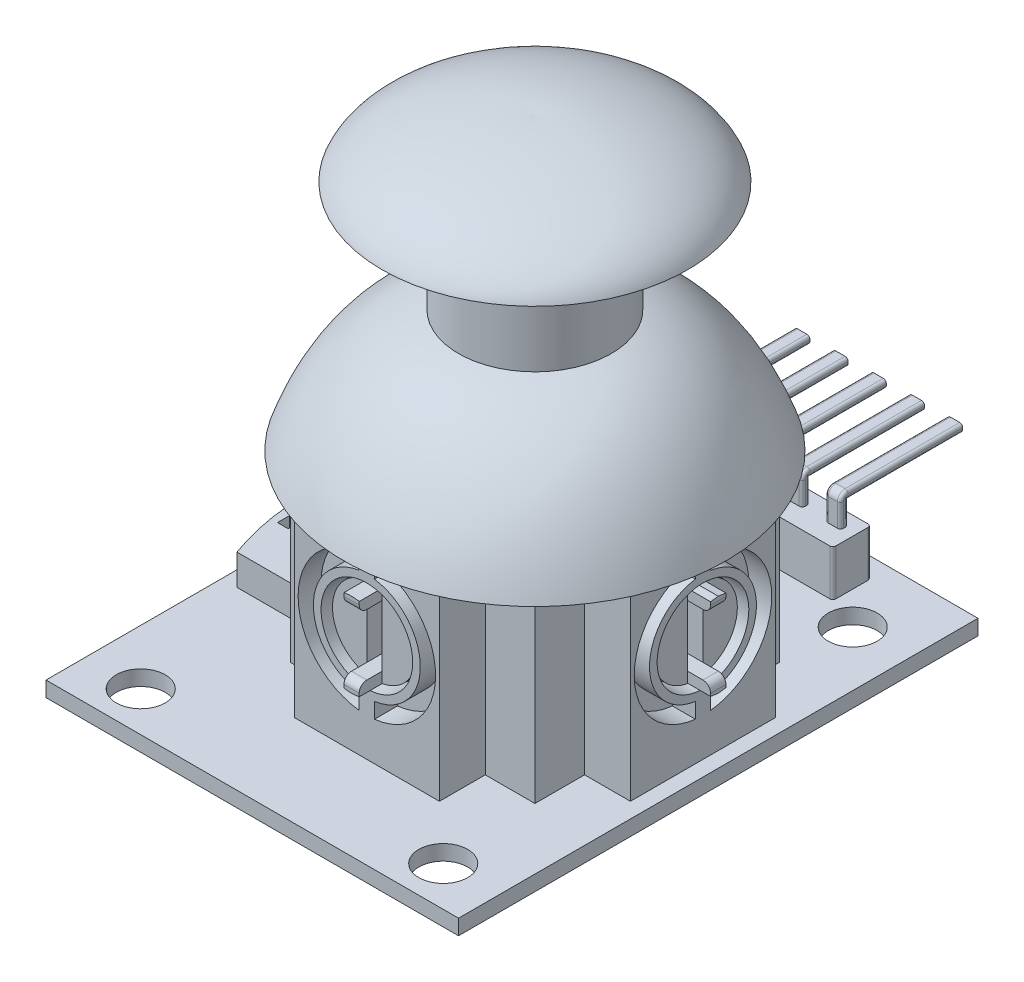
SolidWorks part; units mm, degrees
ref_plane "Ön Düzlem" through (0, 0, 0) normal (0, 0, 1) x (1, 0, 0)
ref_plane "Üst Düzlem" through (0, 0, 0) normal (0, 1, 0) x (1, 0, 0)
ref_plane "Sağ Düzlem" through (0, 0, 0) normal (1, 0, 0) x (0, 0, -1)
sketch "Çizim1" plane through (0, 0, 0) normal (0, 1, 0) x (1, 0, 0)
  line L0 (-13.5, -14.4) -> (13.5, -14.4) construction
  line L1 (-13.5, 17) -> (13.5, 17)
  line L2 (-13.5, 17) -> (-13.5, -17)
  line L3 (-13.5, -17) -> (13.5, -17)
  line L4 (13.5, 17) -> (13.5, -17)
  line L5 (-13.5, 17) -> (13.5, -17) construction
  line L6 (-13.5, -17) -> (13.5, 17) construction
  line L7 (-9.9, 17) -> (-9.9, -17) construction
  line L8 (0, 17) -> (0, -17) construction
  line L9 (-13.5, 12.4) -> (13.5, 12.4) construction
  circle A0 centre (-9.9, -14.4) radius 1.6
  circle A1 centre (9.9, -14.4) radius 1.6
  circle A2 centre (-9.9, 12.4) radius 1.6
  circle A3 centre (9.9, 12.4) radius 1.6
  point P0 (0, 0)
  dimension "D5" = 3.2
  dimension "D7" = 3.2
  dimension "D1" = 27
  dimension "D2" = 34
  dimension "D3" = 2.6
  dimension "D4" = 3.6
  dimension "D6" = 4.6
extrude "Yükseklik-Ekstrüzyon1" add sketch "Çizim1" along normal blind 1
sketch "Çizim2" plane through (0, 1, 0) normal (0, 1, 0) x (1, 0, 0)
  line L0 (9.5, 17) -> (9.5, -17) construction
  line L1 (13.5, 17) -> (-13.5, 17) construction
  line L2 (-13.5, -17) -> (13.5, -17) construction
  line L3 (13.5, -17) -> (13.5, 17) construction
  line L4 (13.5, -8) -> (-13.5, -8) construction
  line L5 (-13.5, 17) -> (-13.5, -17) construction
  line L6 (9.3, -7.8) -> (9.3, 7.8)
  line L7 (9.5, -8) -> (-6.5, -8)
  line L8 (9.5, -8) -> (9.5, 8)
  line L9 (9.5, 8) -> (-6.5, 8)
  line L10 (-6.5, -8) -> (-6.5, 8)
  line L11 (9.3, 7.8) -> (-6.3, 7.8)
  line L12 (-6.3, -7.8) -> (-6.3, 7.8)
  line L13 (9.3, -7.8) -> (-6.3, -7.8)
  dimension "D1" = 4
  dimension "D2" = 9
  dimension "D3" = 16
  dimension "D4" = 16
  dimension "D5" = 0.2
extrude "Yükseklik-Ekstrüzyon2" add sketch "Çizim2" along normal blind 12
sketch "Çizim3" plane through (0, 0, 8) normal (0, 0, 1) x (1, 0, 0)
  line L0 (1.5, 13) -> (1.5, 1) construction
  line L1 (-6.5, 13) -> (9.5, 13) construction
  line L2 (-6.5, 1) -> (9.5, 1) construction
  line L4 (-3.25, 1) -> (6.25, 1)
  line L5 (-3.25, 1) -> (-3.25, 13)
  line L6 (-3.25, 13) -> (6.25, 13)
  line L7 (6.25, 1) -> (6.25, 13)
  line L8 (-3.25, 1) -> (6.25, 13) construction
  line L9 (-3.25, 13) -> (6.25, 1) construction
  point P6 (1.5, 7)
  dimension "D1" = 9.5
extrude "Yükseklik-Ekstrüzyon3" add sketch "Çizim3" along normal blind 3
sketch "Çizim4" plane through (0, 0, 11) normal (0, 0, 1) x (1, 0, 0)
  line L0 (-3.25, 3) -> (6.25, 3) construction
  line L1 (-3.25, 13) -> (-3.25, 1) construction
  line L2 (6.25, 1) -> (6.25, 13) construction
  line L3 (-3.25, 1) -> (6.25, 1) construction
  line L4 (1.5, 13) -> (1.5, 3) construction
  line L6 (1, 12.4721) -> (1, 11.4641)
  line L7 (2, 12.4721) -> (2, 11.4641)
  line L8 (1, 4.5359) -> (1, 3.5279)
  line L9 (2, 4.5359) -> (2, 3.5279)
  circle A0 centre (1.5, 8) radius 5
  arc A1 (1, 11.4641) -> (1, 4.5359) centre (1.5, 8) ccw
  arc A2 (1, 12.4721) -> (1, 3.5279) centre (1.5, 8) ccw
  arc A3 (2, 4.5359) -> (2, 11.4641) centre (1.5, 8) ccw
  arc A4 (2, 3.5279) -> (2, 12.4721) centre (1.5, 8) ccw
  circle A5 centre (1.5, 8) radius 3
  dimension "D2" = 7
  dimension "D3" = 9
  dimension "D8" = 6
  dimension "D1" = 2
  dimension "D4" = 0.5
  dimension "D5" = 0.5
  dimension "D6" = 0.5
  dimension "D7" = 0.5
extrude "Kes-Ekstrüzyon1" cut sketch "Çizim4" against normal blind 1.5 contours L6 A1 L8 A2 | A5 | A4 L7 A3 L9
sketch "Çizim5" plane through (0, 0, 9.5) normal (0, 0, 1) x (1, 0, 0)
  circle A0 centre (1.5, 8) radius 2.75
  dimension "D1" = 5.5
extrude "Yükseklik-Ekstrüzyon4" add sketch "Çizim5" along normal blind 1
sketch "Çizim6" plane through (0, 0, 10.5) normal (0, 0, 1) x (1, 0, 0)
  line L0 (1.5, 10.75) -> (1.5, 5.25) construction
  line L1 (2, 10.7042) -> (2, 10)
  line L2 (1, 10.7042) -> (1, 10)
  line L3 (1, 10) -> (2, 10)
  line L4 (1.5, 8) -> (2, 8) construction
  line L5 (1, 6) -> (2, 6)
  line L6 (1, 6) -> (1, 5.2958)
  line L7 (2, 6) -> (2, 5.2958)
  circle A0 centre (1.5, 8) radius 2.75 construction
  circle A1 centre (1.5, 8) radius 2.75 construction
  arc A2 (1, 5.2958) -> (2, 5.2958) centre (1.5, 8) ccw
  arc A3 (2, 10.7042) -> (1, 10.7042) centre (1.5, 8) ccw
  dimension "D1" = 0.5
  dimension "D2" = 0.75
extrude "Yükseklik-Ekstrüzyon5" add sketch "Çizim6" along normal blind 1.5
fillet "Radyus1" radius 0.5 2 edges at (1.5, 6, 12) (1.5, 10, 12)
sketch "Çizim7" plane through (0, 0, 10.5) normal (0, 0, 1) x (1, 0, 0)
  line L0 (1.5, 10) -> (1.5, 6) construction
  line L1 (1, 10) -> (2, 10) construction
  line L2 (2, 6) -> (1, 6) construction
  line L4 (1, 10) -> (2, 10)
  line L5 (1, 10) -> (1, 6)
  line L6 (1, 6) -> (2, 6)
  line L7 (2, 10) -> (2, 6)
  line L8 (1, 10) -> (2, 6) construction
  line L9 (1, 6) -> (2, 10) construction
  point P6 (1.5, 8)
extrude "Kes-Ekstrüzyon2" cut sketch "Çizim7" against normal blind 1.5
sketch "Çizim8" plane through (0, 1, 0) normal (0, 1, 0) x (1, 0, 0)
  line L0 (-6.5, 0) -> (-13.5, 0) construction
  line L1 (-6.5, 8) -> (-6.5, -8) construction
  line L2 (-13.5, 17) -> (-13.5, -17) construction
  line L3 (-6.5, 8) -> (-6.5, -8) construction
  line L4 (-12.5, 5.5) -> (-6.5, 5.5)
  line L6 (-12.5, -5.5) -> (-6.5, -5.5)
  line L7 (-6.5, 5.5) -> (-6.5, -5.5)
  line L8 (-13.5, 5.5) -> (-6.5, -5.5) construction
  line L9 (-13.5, -5.5) -> (-6.5, 5.5) construction
  line L10 (-12.5, 5.5) -> (-12.5, -5.5) construction
  line L12 (-12.85, 2.5) -> (-12.15, 2.5)
  line L13 (-12.85, 2.5) -> (-12.85, -2.5)
  line L14 (-12.85, -2.5) -> (-12.15, -2.5)
  line L15 (-12.15, 2.5) -> (-12.15, -2.5)
  line L16 (-12.85, 2.5) -> (-12.15, -2.5) construction
  line L17 (-12.85, -2.5) -> (-12.15, 2.5) construction
  spline S0 degree 2 poles (-12.5, 5.5) (-14.5, 0) (-12.5, -5.5) knots 0 0 0 1 1 1
  point P6 (-10, 0)
  point P15 (-12.5, 0)
  dimension "D1" = 11
  dimension "D2" = 5
  dimension "D3" = 0.7
extrude "Yükseklik-Ekstrüzyon6" add sketch "Çizim8" along normal blind 2
sketch "Çizim9" plane through (0, 3, 0) normal (0, 1, 0) x (1, 0, 0)
  line L0 (-6.3, 0) -> (-12.15, 0) construction
  line L1 (-6.3, 7.8) -> (-6.3, -7.8) construction
  line L2 (-12.15, -2.5) -> (-12.15, 2.5) construction
  line L4 (-12.15, 2.3967) -> (-6.3, 2.3967)
  line L5 (-12.15, 2.3967) -> (-12.15, -2.3967)
  line L6 (-12.15, -2.3967) -> (-6.3, -2.3967)
  line L7 (-6.3, 2.3967) -> (-6.3, -2.3967)
  line L8 (-12.15, 2.3967) -> (-6.3, -2.3967) construction
  line L9 (-12.15, -2.3967) -> (-6.3, 2.3967) construction
  point P6 (-9.225, 0)
extrude "Yükseklik-Ekstrüzyon7" add sketch "Çizim9" along normal blind 1
sketch "Çizim10" plane through (0, 4, 0) normal (0, 1, 0) x (1, 0, 0)
  line L0 (-6.5, 0) -> (-12.15, 0) construction
  line L1 (-6.5, 2.3967) -> (-6.5, -2.3967) construction
  line L2 (-12.15, 2.3967) -> (-12.15, -2.3967) construction
  line L4 (-12.15, 2.3967) -> (-6.5, 2.3967)
  line L5 (-12.15, 2.3967) -> (-12.15, -2.3967)
  line L6 (-12.15, -2.3967) -> (-6.5, -2.3967)
  line L7 (-6.5, 2.3967) -> (-6.5, -2.3967)
  line L8 (-12.15, 2.3967) -> (-6.5, -2.3967) construction
  line L9 (-12.15, -2.3967) -> (-6.5, 2.3967) construction
  point P6 (-9.325, 0)
extrude "Yükseklik-Ekstrüzyon8" add sketch "Çizim10" along normal blind 0.2
sketch "Çizim11" plane through (0, 4.2, 0) normal (0, 1, 0) x (1, 0, 0)
  line L0 (-12.15, 2.3967) -> (-6.5, -2.3967) construction
  line L1 (-6.5, -2.3967) -> (-6.5, 2.3967) construction
  line L2 (-6.5, 2.3967) -> (-12.15, -2.3967) construction
  line L3 (-12.15, -2.3967) -> (-12.15, 0) construction
  line L4 (-12.15, -2.5) -> (-12.15, 2.5) construction
  line L5 (-12.15, 0) -> (-6.5, 0) construction
  line L6 (-6.5, 0) -> (-9.325, 0) construction
  line L7 (-9.325, 0) -> (-9.325, 2.3967) construction
  line L8 (-6.5, 2.3967) -> (-12.15, 2.3967) construction
  line L9 (-6.5, 2.3967) -> (-12.15, 2.3967) construction
  circle A0 centre (-11.7964, 2.0967) radius 0.15
  circle A1 centre (-6.8536, 2.0967) radius 0.15
  circle A2 centre (-6.8536, -2.0967) radius 0.15
  circle A3 centre (-11.7964, -2.0967) radius 0.15
  dimension "D1" = 0.3
  dimension "D2" = 0.3
extrude "Yükseklik-Ekstrüzyon9" add sketch "Çizim11" along normal blind 0.1
sketch "Çizim12" plane through (0, 4.2, 0) normal (0, 1, 0) x (1, 0, 0)
  line L0 (-12.15, 0) -> (-6.5, 0) construction
  line L1 (-12.15, -2.5) -> (-12.15, 2.5) construction
  line L2 (-6.5, -2.3967) -> (-6.5, 2.3967) construction
  circle A0 centre (-9.325, 0) radius 1.75
  dimension "D1" = 3.5
extrude "Yükseklik-Ekstrüzyon10" add sketch "Çizim12" along normal blind 2
ref_plane "Düzlem1" through (-6.5, 0, 0) normal (-1, 0, 0) x (0, 0, 1)
sketch "Çizim13" plane through (-6.5, 0, 0) normal (-1, 0, 0) x (0, 0, 1)
  line L0 (0, 1) -> (0, 6.2) construction
  line L1 (1.75, 6.2) -> (-1.75, 6.2) construction
  line L2 (0, 1) -> (17, 1) construction
  line L3 (-3.5, 6.2) -> (-1.9261, 6.2)
  line L4 (-4, 5.7) -> (-4, 1)
  line L5 (-4, 1) -> (4, 1)
  line L6 (4, 5.7) -> (4, 1)
  line L7 (-4, 6.2) -> (4, 1) construction
  line L8 (-4, 1) -> (4, 6.2) construction
  line L9 (-4, 5.5) -> (4, 5.5) construction
  line L10 (0, 5.5) -> (0, 8.5) construction
  line L11 (1.9261, 6.2) -> (3.5, 6.2)
  arc A0 (1.9261, 6.2) -> (-1.9261, 6.2) centre (0, 8.5) ccw
  arc A1 (3.5, 6.2) -> (4, 5.7) centre (3.5, 5.7) cw
  arc A2 (-3.5, 6.2) -> (-4, 5.7) centre (-3.5, 5.7) ccw
  point P5 (0, 3.6)
  dimension "D4" = 0.5
  dimension "D1" = 8
  dimension "D2" = 0.7
  dimension "D3" = 3
extrude "Kes-Ekstrüzyon3" cut sketch "Çizim13" against normal blind 2
sketch "Çizim14" plane through (0, 1, 0) normal (0, 1, 0) x (1, 0, 0)
  line L0 (-6.3, 7.8) -> (9.3, -7.8) construction
  line L1 (9.3, -7.8) -> (9.3, 7.8) construction
  line L2 (9.3, 7.8) -> (-6.3, -7.8) construction
  circle A0 centre (1.5, 0) radius 1.5
  dimension "D1" = 3
extrude "Yükseklik-Ekstrüzyon11" add sketch "Çizim14" along normal blind 31
ref_plane "Düzlem2" through (1.5, 0, 0) normal (1, 0, 0) x (0, 0, -1)
sketch "Çizim15" plane through (1.5, 0, 0) normal (1, 0, 0) x (0, 0, -1)
  line L0 (0, 11.5) -> (0, 5.5) construction
  line L1 (1.75, 6.2) -> (-1.75, 6.2) construction
  arc A0 (1.9261, 6.2) -> (-1.9261, 6.2) centre (0, 8.5) ccw construction
  circle A1 centre (0, 8.5) radius 1.4
  dimension "D2" = 2.8
  dimension "D1" = 0.7
extrude "Yükseklik-Ekstrüzyon12" add sketch "Çizim15" against normal blind 8
sketch "Çizim17" plane through (-6.5, 0, 0) normal (-1, 0, 0) x (0, 0, 1)
  circle A0 centre (0, 8.5) radius 2.15
  dimension "D1" = 4.3
extrude "Yükseklik-Ekstrüzyon14" add sketch "Çizim17" along normal blind 2
sketch "Çizim18" plane through (-8.5, 0, 0) normal (-1, 0, 0) x (0, 0, 1)
  line L0 (1, 8.5) -> (1, 10.6)
  line L1 (0, 8.5) -> (0, 10.1842) construction
  line L2 (-1, 8.5) -> (-1, 10.6)
  line L3 (-0.8, 10.8) -> (0.8, 10.8)
  arc A0 (-1, 8.5) -> (1, 8.5) centre (0, 8.5) ccw
  arc A1 (1, 10.6) -> (0.8, 10.8) centre (0.8, 10.6) ccw
  arc A2 (-1, 10.6) -> (-0.8, 10.8) centre (-0.8, 10.6) cw
  point P10 (1, 10.8)
  point P13 (-1, 10.8)
  dimension "D1" = 2
  dimension "D3" = 0.2
  dimension "D2" = 2.3
extrude "Yükseklik-Ekstrüzyon15" add sketch "Çizim18" along normal blind 1
sketch "Çizim19" plane through (1.5, 0, 0) normal (1, 0, 0) x (0, 0, -1)
  line L0 (0, 13) -> (0, 32) construction
  line L1 (-8, 13) -> (8, 13) construction
  line L2 (1.5, 32) -> (-1.5, 32) construction
  line L3 (0, 13) -> (-12.5, 13) construction
  line L4 (0, 21) -> (-8.523, 21) construction
  line L5 (-5, 21) -> (-5, 28.2501) construction
  line L6 (-5, 28.2501) -> (-5, 21)
  line L7 (0, 28.2501) -> (-5, 28.2501) construction
  line L8 (-4.8, 28.2501) -> (-4.8, 21)
  line L9 (-4.8, 21) -> (-4.8, 20.8071)
  line L10 (-4.8, 20.8071) -> (-4.9473, 20.8071)
  line L11 (-4.8, 28.2501) -> (-5, 28.2501)
  line L12 (-12.5, 13) -> (-12.2881, 13)
  spline S0 degree 2 poles (-12.5, 13) (-10.2136, 19.5749) (-5, 21) knots 0 0 0 0.911664 0.911664 0.911664
  spline S1 degree 1 poles (-12.3111, 12.9343) (-4.9473, 20.8071) knots 0 0 1 1 construction
  spline S2 degree 3 poles (-12.3111, 12.9343) (-12.129, 13.4581) (-11.7118, 14.5176) (-11.0157, 15.8911) (-10.2263, 17.1167) (-9.0588, 18.5307) (-7.7136, 19.6264) (-6.1973, 20.4046) (-5.3666, 20.6925) (-4.9473, 20.8071) knots 0 0 0 0 0.113958 0.227916 0.341874 0.455832 0.683748 0.797706 0.911664 0.911664 0.911664 0.911664 only from (-12.2881, 13) to (-4.9473, 20.8071)
  dimension "D1" = 12.5
  dimension "D2" = 8
  dimension "D3" = 5
  dimension "D4" = 0.2
  dimension "D5" = 0.2
revolve "Döndür1" add sketch "Çizim19" angle 360 about L0
sketch "Çizim21" plane through (1.5, 0, 0) normal (1, 0, 0) x (0, 0, -1)
  line L0 (0, 32) -> (0, 31.8005)
  line L1 (5, 28.2501) -> (-5, 28.2501) construction
  line L2 (1.5, 32) -> (-1.5, 32) construction
  line L3 (0, 31.8005) -> (-0.0142, 31.8005)
  line L4 (0, 28.2501) -> (-10, 28.2501) construction
  line L5 (-10, 28.2501) -> (-4.4061, 28.2501)
  line L6 (-9.6822, 28.4501) -> (-4.4061, 28.4501)
  line L8 (-4.4061, 28.4501) -> (-4.4061, 28.2501)
  line L9 (0, 28.2501) -> (0, 32) construction
  spline S0 degree 3 poles (0, 32) (-0.7458, 32.053) (-4.5905, 31.8985) (-9.2203, 30.199) (-10, 28.2501) knots 0 0 0 0 0.179556 0.797541 0.797541 0.797541 0.797541
  spline S1 degree 1 poles (-0.0142, 31.8005) (-9.6822, 28.4501) knots 0 0 1 1 construction
  spline S2 degree 3 poles (-0.0142, 31.8005) (-0.2164, 31.8149) (-0.6109, 31.8296) (-1.4874, 31.8134) (-2.6583, 31.7055) (-4.1279, 31.4449) (-5.5814, 31.0596) (-6.9454, 30.5576) (-8.1444, 29.947) (-8.9413, 29.3605) (-9.4244, 28.8478) (-9.6032, 28.5901) (-9.6822, 28.4501) knots 0 0 0 0 0.047842 0.095684 0.191367 0.287051 0.382735 0.478418 0.574102 0.669786 0.717628 0.765469 0.765469 0.765469 0.765469
  point P6 (-1.5, 32)
  dimension "D1" = 10
  dimension "D2" = 0.2
revolve "Döndür3" add sketch "Çizim21" angle 360 about L9
sketch "Çizim22" plane through (9.5, 0, 0) normal (1, 0, 0) x (0, 0, -1)
  line L0 (0, 13) -> (0, 1) construction
  line L1 (-8, 13) -> (8, 13) construction
  line L2 (-17, 1) -> (17, 1) construction
  line L3 (-8, 1) -> (8, 1) construction
  line L4 (-4.75, 13) -> (4.75, 13)
  line L5 (-4.75, 13) -> (-4.75, 1)
  line L6 (-4.75, 1) -> (4.75, 1)
  line L7 (4.75, 13) -> (4.75, 1)
  line L8 (-4.75, 13) -> (4.75, 1) construction
  line L9 (-4.75, 1) -> (4.75, 13) construction
  point P6 (0, 7)
  dimension "D1" = 9.5
extrude "Yükseklik-Ekstrüzyon16" add sketch "Çizim22" along normal blind 3
sketch "Çizim23" plane through (12.5, 0, 0) normal (1, 0, 0) x (0, 0, -1)
  line L0 (-4.75, 3) -> (4.75, 3) construction
  line L1 (-4.75, 13) -> (-4.75, 1) construction
  line L2 (4.75, 1) -> (4.75, 13) construction
  line L3 (-4.75, 1) -> (4.75, 1) construction
  line L4 (0, 3) -> (0, 13) construction
  line L5 (4.75, 13) -> (-4.75, 13) construction
  line L6 (-0.5, 12.4721) -> (-0.5, 11.4641)
  line L7 (0.5, 12.4721) -> (0.5, 11.4641)
  line L8 (0, 8) -> (1.7339, 8) construction
  line L9 (0.5, 3.5279) -> (0.5, 4.5359)
  line L10 (-0.5, 3.5279) -> (-0.5, 4.5359)
  arc A0 (-0.5, 12.4721) -> (-0.5, 3.5279) centre (0, 8) ccw
  arc A1 (-0.5, 11.4641) -> (-0.5, 4.5359) centre (0, 8) ccw
  arc A2 (0.5, 4.5359) -> (0.5, 11.4641) centre (0, 8) ccw
  arc A3 (0.5, 3.5279) -> (0.5, 12.4721) centre (0, 8) ccw
  point P19 (0.5, 11.9681)
  dimension "D2" = 9
  dimension "D3" = 7
  dimension "D1" = 2
  dimension "D4" = 0.5
  dimension "D5" = 0.5
extrude "Kes-Ekstrüzyon4" cut sketch "Çizim23" against normal blind 1.5
sketch "Çizim24" plane through (12.5, 0, 0) normal (1, 0, 0) x (0, 0, -1)
  line L0 (0, 13) -> (0, 1) construction
  line L1 (4.75, 13) -> (-4.75, 13) construction
  line L2 (-4.75, 1) -> (4.75, 1) construction
  circle A0 centre (0, 8) radius 3
  dimension "D1" = 6
extrude "Kes-Ekstrüzyon5" cut sketch "Çizim24" against normal blind 1.5
sketch "Çizim25" plane through (11, 0, 0) normal (1, 0, 0) x (0, 0, -1)
  circle A0 centre (0, 8) radius 2.75
  dimension "D1" = 5.5
extrude "Yükseklik-Ekstrüzyon17" add sketch "Çizim25" along normal blind 1
sketch "Çizim26" plane through (12, 0, 0) normal (1, 0, 0) x (0, 0, -1)
  line L0 (0, 10) -> (0, 5.25) construction
  line L1 (0, 10) -> (0.5, 10) construction
  line L3 (0.5, 10) -> (-0.5, 10)
  line L4 (0.5, 10) -> (0.5, 10.6836)
  line L8 (-0.5, 10) -> (-0.5, 10.6836)
  line L9 (0, 10.75) -> (0, 5.25) construction
  line L10 (0, 8) -> (0.891, 8) construction
  line L12 (0.5, 6) -> (0.5, 5.3167)
  line L13 (0.5, 6) -> (-0.5, 6)
  line L14 (-0.5, 6) -> (-0.5, 5.3167)
  line L16 (0, 10.75) -> (0.5, 10.6836)
  line L17 (0, 10.75) -> (-0.5, 10.6836)
  line L18 (0, 5.25) -> (-0.5, 5.3167)
  line L19 (0, 5.25) -> (0.5, 5.3167)
  circle A0 centre (0, 8) radius 2.75 construction
  circle A1 centre (0, 8) radius 2.75 construction
  dimension "D1" = 0.75
  dimension "D2" = 0.5
extrude "Yükseklik-Ekstrüzyon18" add sketch "Çizim26" along normal blind 1.5
fillet "Radyus2" radius 0.5 2 edges at (13.5, 6, 0) (13.5, 10, 0)
sketch "Çizim27" plane through (12, 0, 0) normal (1, 0, 0) x (0, 0, -1)
  line L0 (0, 10) -> (0, 6) construction
  line L1 (-0.5, 10) -> (0.5, 10) construction
  line L2 (0.5, 6) -> (-0.5, 6) construction
  line L4 (-0.5, 10) -> (0.5, 10)
  line L5 (-0.5, 10) -> (-0.5, 6)
  line L6 (-0.5, 6) -> (0.5, 6)
  line L7 (0.5, 10) -> (0.5, 6)
  line L8 (-0.5, 10) -> (0.5, 6) construction
  line L9 (-0.5, 6) -> (0.5, 10) construction
  point P6 (0, 8)
extrude "Kes-Ekstrüzyon6" cut sketch "Çizim27" against normal blind 1.5
sketch "Çizim28" plane through (0, 0, -8) normal (0, 0, -1) x (-1, 0, 0)
  line L0 (-1.5, 1) -> (-1.5, 8) construction
  line L1 (-9.5, 1) -> (6.5, 1) construction
  line L2 (-13.5, 1) -> (13.5, 1) construction
  line L3 (-5, 8) -> (-3.5, 8)
  line L4 (-5.5, 7.5) -> (-5.5, 1)
  line L5 (-5.5, 1) -> (2.5, 1)
  line L6 (2.5, 7.5) -> (2.5, 1)
  line L7 (-5.5, 8) -> (2.5, 1) construction
  line L8 (-5.5, 1) -> (2.5, 8) construction
  line L9 (0.5, 8) -> (2, 8)
  line L11 (-3.5, 8) -> (-3.5, 7)
  line L12 (-3.5, 7) -> (0.5, 7)
  line L13 (0.5, 8) -> (0.5, 7)
  line L14 (-3.5, 9) -> (0.5, 7) construction
  line L15 (-3.5, 7) -> (0.5, 9) construction
  line L16 (-5.5, 7.5) -> (-5, 8)
  line L17 (2, 8) -> (2.5, 7.5)
  point P4 (-1.5, 4.5)
  dimension "D1" = 7
  dimension "D2" = 8
  dimension "D3" = 2
  dimension "D4" = 4
extrude "Yükseklik-Ekstrüzyon19" add sketch "Çizim28" along normal blind 1
sketch "Çizim29" plane through (0, 1, 0) normal (0, 1, 0) x (1, 0, 0)
  line L0 (-13.5, 14.5) -> (13.5, 14.5) construction
  line L1 (-13.5, 17) -> (-13.5, 0) construction
  line L2 (13.5, -17) -> (13.5, 17) construction
  line L3 (13.5, 17) -> (-13.5, 17) construction
  line L4 (1.5, 17) -> (1.5, 14.5) construction
  line L6 (-4.55, 15.75) -> (7.55, 15.75)
  line L7 (-4.75, 15.55) -> (-4.75, 13.45)
  line L8 (-4.55, 13.25) -> (7.55, 13.25)
  line L9 (7.75, 15.55) -> (7.75, 13.45)
  line L10 (-4.75, 15.75) -> (7.75, 13.25) construction
  line L11 (-4.75, 13.25) -> (7.75, 15.75) construction
  arc A0 (7.55, 13.25) -> (7.75, 13.45) centre (7.55, 13.45) ccw
  arc A1 (7.55, 15.75) -> (7.75, 15.55) centre (7.55, 15.55) cw
  arc A2 (-4.75, 13.45) -> (-4.55, 13.25) centre (-4.55, 13.45) ccw
  arc A3 (-4.55, 15.75) -> (-4.75, 15.55) centre (-4.55, 15.55) ccw
  dimension "D5" = 0.2
  dimension "D1" = 2.5
  dimension "D2" = 12
  dimension "D3" = 12.5
  dimension "D4" = 2.5
extrude "Yükseklik-Ekstrüzyon20" add sketch "Çizim29" along normal blind 3
ref_plane "Düzlem3" through (1.5, 0, 0) normal (1, 0, 0) x (0, 0, -1)
sketch "Çizim30" plane through (1.5, 0, 0) normal (1, 0, 0) x (0, 0, -1)
  line L0 (14.5, 4) -> (14.5, 5.5)
  line L1 (13.45, 4) -> (15.55, 4) construction
  line L2 (15, 6) -> (22.5, 6)
  line L3 (15, 4) -> (15, 5.5)
  line L4 (15, 5.5) -> (22.5, 5.5)
  line L5 (22.5, 6) -> (22.5, 5.5)
  line L6 (15, 4) -> (14.5, 4)
  arc A0 (14.5, 5.5) -> (15, 6) centre (15, 5.5) cw
  arc A1 (15, 5.5) -> (15, 5.5) centre (15, 5.5) cw
  point P7 (14.5, 6)
  dimension "D3" = 0.5
  dimension "D1" = 2
  dimension "D2" = 8
  dimension "D4" = 0.5
extrude "Yükseklik-Ekstrüzyon21" add sketch "Çizim30" along normal blind 0.5 and the other way blind 0.5
ref_plane "Düzlem4" through (4, 0, 0) normal (1, 0, 0) x (0, 0, -1)
sketch "Çizim31" plane through (4, 0, 0) normal (1, 0, 0) x (0, 0, -1)
  line L0 (14.5, 4) -> (14.5, 5.5)
  line L1 (13.45, 4) -> (15.55, 4) construction
  line L2 (15, 6) -> (22.5, 6)
  line L3 (15, 5.5) -> (22.5, 5.5)
  line L4 (22.5, 5.5) -> (22.5, 6)
  line L5 (14.5, 4) -> (15, 4)
  line L6 (15, 4) -> (15, 5.5) construction
  line L7 (15, 5.5) -> (15, 4)
  arc A0 (14.5, 5.5) -> (15, 6) centre (15, 5.5) cw
  dimension "D1" = 0.5
extrude "Yükseklik-Ekstrüzyon22" add sketch "Çizim31" along normal blind 0.5 and the other way blind 0.5
ref_plane "Düzlem5" through (6.5, 0, 0) normal (1, 0, 0) x (0, 0, -1)
sketch "Çizim33" plane through (6.5, 0, 0) normal (1, 0, 0) x (0, 0, -1)
  line L0 (14.5, 4) -> (14.5, 5.5)
  line L1 (13.45, 4) -> (15.55, 4) construction
  line L2 (15, 6) -> (22.5, 6)
  line L3 (15, 4) -> (15, 5.5)
  line L4 (15, 5.5) -> (22.5, 5.5)
  line L5 (22.5, 6) -> (22.5, 5.5)
  line L6 (14.5, 4) -> (15, 4)
  arc A0 (14.5, 5.5) -> (15, 6) centre (15, 5.5) cw
  arc A1 (15, 5.5) -> (15, 5.5) centre (15, 5.5) cw
  dimension "D1" = 0.5
  dimension "D2" = 0.5
extrude "Yükseklik-Ekstrüzyon23" add sketch "Çizim33" along normal blind 0.5 and the other way blind 0.5
ref_plane "Düzlem6" through (-1, 0, 0) normal (1, 0, 0) x (0, 0, -1)
sketch "Çizim34" plane through (-1, 0, 0) normal (1, 0, 0) x (0, 0, -1)
  line L0 (14.5, 4) -> (14.5, 5.5)
  line L1 (13.45, 4) -> (15.55, 4) construction
  line L2 (15, 6) -> (22.5, 6)
  line L3 (15, 4) -> (15, 5.5)
  line L4 (15, 5.5) -> (22.5, 5.5)
  line L5 (14.5, 4) -> (15, 4)
  line L6 (22.5, 6) -> (22.5, 5.5)
  arc A0 (14.5, 5.5) -> (15, 6) centre (15, 5.5) cw
  arc A1 (15, 5.5) -> (15, 5.5) centre (15, 5.5) cw
  dimension "D1" = 0.5
  dimension "D2" = 0.5
extrude "Yükseklik-Ekstrüzyon24" add sketch "Çizim34" along normal blind 0.5 and the other way blind 0.5
ref_plane "Düzlem7" through (-3.5, 0, 0) normal (1, 0, 0) x (0, 0, -1)
sketch "Çizim35" plane through (-3.5, 0, 0) normal (1, 0, 0) x (0, 0, -1)
  line L0 (14.5, 4) -> (14.5, 5.5)
  line L1 (13.45, 4) -> (15.55, 4) construction
  line L2 (15, 6) -> (22.5, 6)
  line L3 (15, 4) -> (15, 5.5)
  line L4 (15, 5.5) -> (22.5, 5.5)
  line L5 (22.5, 6) -> (22.5, 5.5)
  line L6 (14.5, 4) -> (15, 4)
  arc A0 (14.5, 5.5) -> (15, 6) centre (15, 5.5) cw
  arc A1 (15, 5.5) -> (15, 5.5) centre (15, 5.5) cw
  dimension "D1" = 0.5
  dimension "D2" = 0.5
extrude "Yükseklik-Ekstrüzyon25" add sketch "Çizim35" along normal blind 0.5 and the other way blind 0.5
fillet "Radyus3" radius 0.2 50 edges at (6, 4.75, -14.5) (6, 5.8536, -14.6464) (7, 4.75, -14.5) (7, 5.8536, -14.6464) (6, 4.75, -15) (6, 5.5, -18.75) (6, 6, -18.75) (7, 5.5, -18.75) (7, 4.75, -15) (7, 6, -18.75) (-4, 6, -18.75) (-4, 5.8536, -14.6464) (-3, 6, -18.75) (-3, 5.8536, -14.6464) (-1.5, 5.8536, -14.6464) (-0.5, 6, -18.75) (-0.5, 5.8536, -14.6464) (2, 4.75, -14.5) (2, 5.8536, -14.6464) (1, 4.75, -14.5) (1, 5.8536, -14.6464) (3.5, 4.75, -14.5) (3.5, 5.8536, -14.6464) (4.5, 4.75, -14.5) (4.5, 5.8536, -14.6464) (-4, 5.5, -18.75) (-4, 4.75, -14.5) (-4, 4.75, -15) (-3, 5.5, -18.75) (-3, 4.75, -14.5) (-3, 4.75, -15) (-1.5, 6, -18.75) (-1.5, 5.5, -18.75) (-1.5, 4.75, -15) (-1.5, 4.75, -14.5) (-0.5, 5.5, -18.75) (-0.5, 4.75, -15) (-0.5, 4.75, -14.5) (2, 6, -18.75) (2, 5.5, -18.75) (2, 4.75, -15) (1, 6, -18.75) (1, 5.5, -18.75) (1, 4.75, -15) (3.5, 4.75, -15) (3.5, 5.5, -18.75) (3.5, 6, -18.75) (4.5, 6, -18.75) (4.5, 5.5, -18.75) (4.5, 4.75, -15)
